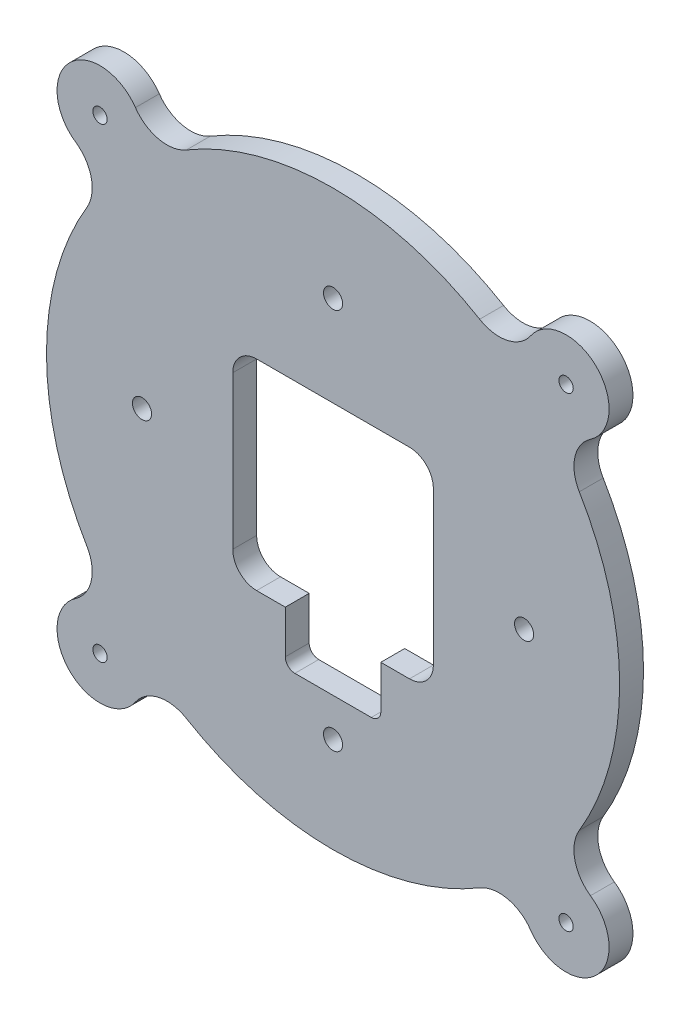
SolidWorks part; units mm, degrees
ref_plane "Front Plane" through (0, 0, 0) normal (0, 0, 1) x (1, 0, 0)
ref_plane "Top Plane" through (0, 0, 0) normal (0, 1, 0) x (1, 0, 0)
ref_plane "Right Plane" through (0, 0, 0) normal (1, 0, 0) x (0, 0, -1)
sketch "Sketch1" plane through (0, 0, 0) normal (0, 1, 0) x (1, 0, 0)
  line L0 (0, 0) -> (69, 0) construction
  line L1 (0, 0) -> (48.7904, 48.7904) construction
  line L2 (10, -21) -> (10, -30.0001)
  line L3 (-16.0057, -21) -> (-10, -21)
  line L4 (-21, -16) -> (-21, 16)
  line L5 (-16, 21) -> (16, 21)
  line L6 (21.0004, -16.0016) -> (21.0004, 16.0016)
  line L7 (0, 21) -> (0, -21) construction
  line L8 (-21, 0) -> (21.0004, 0) construction
  line L9 (8, -32.0001) -> (-8.0002, -32.0001)
  line L10 (-10, -30.0001) -> (-10, -21)
  line L11 (10, -21) -> (16.0019, -21)
  line L12 (0, 0) -> (0, 40) construction
  arc A0 (30.694, 51.5546) -> (-30.694, 51.5546) centre (0, 0) ccw
  circle A1 centre (0, 0) radius 69 construction
  circle A2 centre (0, 0) radius 68 construction
  arc A3 (53.8929, 41.3766) -> (41.3766, 53.8929) centre (48.7904, 48.7904) ccw
  arc A5 (53.9387, 41.4079) -> (51.5546, 30.694) centre (58.4285, 34.7866) ccw
  circle A6 centre (0, 0) radius 69 construction
  arc A7 (41.3766, -53.8929) -> (53.8929, -41.3766) centre (48.7904, -48.7904) ccw
  circle A8 centre (0, 0) radius 69 construction
  arc A9 (-53.8929, -41.3766) -> (-41.3766, -53.8929) centre (-48.7904, -48.7904) ccw
  circle A10 centre (0, 0) radius 69 construction
  arc A11 (-41.3766, 53.8929) -> (-53.8929, 41.3766) centre (-48.7904, 48.7904) ccw
  circle A12 centre (0, 0) radius 68 construction
  arc A13 (51.5546, -30.694) -> (53.8929, -41.3766) centre (58.4285, -34.7866) ccw
  circle A15 centre (0, 0) radius 68 construction
  arc A17 (-53.9387, -41.4079) -> (-51.5546, -30.694) centre (-58.4285, -34.7866) ccw
  circle A18 centre (0, 0) radius 68 construction
  arc A20 (-41.4079, 53.9387) -> (-30.694, 51.5546) centre (-34.7866, 58.4285) ccw
  circle A21 centre (0, 0) radius 40 construction
  circle A22 centre (0, 40) radius 2
  circle A23 centre (0, 0) radius 40 construction
  circle A24 centre (40, 0) radius 2
  circle A25 centre (0, 0) radius 40 construction
  circle A26 centre (0, -40) radius 2
  circle A27 centre (0, 0) radius 40 construction
  circle A28 centre (-40, 0) radius 2
  arc A29 (-21, 16) -> (-16, 21) centre (-16, 16) cw
  arc A30 (21.0004, 16.0016) -> (16, 21) centre (16.001, 16.0006) ccw
  arc A31 (-21, -16) -> (-16.0057, -21) centre (-16.0029, -16.0029) ccw
  arc A32 (21.0004, -16.0016) -> (16.0019, -21) centre (16.0019, -16.0016) cw
  arc A33 (-10, -30.0001) -> (-8.0002, -32.0001) centre (-8.0001, -30.0002) ccw
  arc A34 (10, -30.0001) -> (8, -32.0001) centre (8, -30.0001) cw
  circle A35 centre (-48.7904, -48.7904) radius 1.5
  circle A36 centre (0, 0) radius 69 construction
  circle A37 centre (-48.7904, 48.7904) radius 1.5
  circle A38 centre (0, 0) radius 69 construction
  circle A39 centre (48.7904, 48.7904) radius 1.5
  circle A40 centre (0, 0) radius 69 construction
  circle A41 centre (48.7904, -48.7904) radius 1.5
  arc A42 (30.694, 51.5546) -> (41.3766, 53.8929) centre (34.7866, 58.4285) ccw
  arc A43 (-51.5546, 30.694) -> (-51.5546, -30.694) centre (0, 0) ccw
  arc A44 (-51.5546, 30.694) -> (-53.8929, 41.3766) centre (-58.4285, 34.7866) ccw
  arc A45 (-30.694, -51.5546) -> (30.694, -51.5546) centre (0, 0) ccw
  arc A46 (-30.694, -51.5546) -> (-41.3766, -53.8929) centre (-34.7866, -58.4285) ccw
  arc A47 (41.3766, -53.8929) -> (30.694, -51.5546) centre (34.7866, -58.4285) ccw
  arc A48 (27.6838, -62.1096) -> (28.2027, -62.9731) centre (34.7866, -58.4285) ccw [skipped]
  arc A49 (51.5546, -30.694) -> (51.5546, 30.694) centre (0, 0) ccw
  point P24 (0, 0)
  point P40 (0, 0)
  point P64 (0, 0)
  point P90 (0, 0)
  point P91 (0, 0)
  dimension "D1" = 120
  dimension "D2" = 138
  dimension "D3" = 136
  dimension "D4" = 18
  dimension "D5" = 68
  dimension "D6" = 16
  dimension "D15" = 80
  dimension "D16" = 4
  dimension "D18" = 90
  dimension "D19" = 5
  dimension "D20" = 90
  dimension "D21" = 4.9994
  dimension "D22" = 90
  dimension "D23" = 4.9971
  dimension "D24" = 90
  dimension "D25" = 4.9984
  dimension "D26" = 90
  dimension "D27" = 1.9999
  dimension "D28" = 90
  dimension "D29" = 2
  dimension "D10" = 3
  dimension "D7" = 45
  dimension "D11" = 4
  dimension "D12" = 20
  dimension "D13" = 6.0019
  dimension "D14" = 42.0004
  dimension "D17" = 4
  dimension "D30" = 16.0001
  dimension "D31" = 42
  dimension "D32" = 32
  dimension "D33" = 32.0077
  dimension "D34" = 10.6826
  dimension "D35" = 32
  dimension "D36" = 20
  dimension "D37" = 30.0002
  dimension "D38" = 8
  dimension "D39" = 10.6826
  dimension "D40" = 8
  dimension "D41" = 10.6826
  dimension "D42" = 8
  dimension "D43" = 68
  dimension "D44" = 10.6826
  dimension "D45" = 8
  dimension "D46" = 68
  dimension "D47" = 68
  dimension "D48" = 10.6826
  dimension "D49" = 8
  dimension "D8" = 4
  dimension "D9" = 4
extrude "Boss-Extrude1" add sketch "Sketch1" along normal blind 5 contours A13 A49 A5 A3 A42 A0 A20 A11 A44 A43 A17 A9 A46 A45 A47 A7 L2 A34 L9 A33 L10 L3 A31 L4 A29 L5 A30 L6 A32 L11 A22 A24 A26 A28 A35 A37 A39 A41
move or copy body "Body-Move/Copy1" bodies to move or copy 101 copy no rotation origin (0, 2.5, 0.1609) rotation axis (1, 0, 0) rotation angle 90
